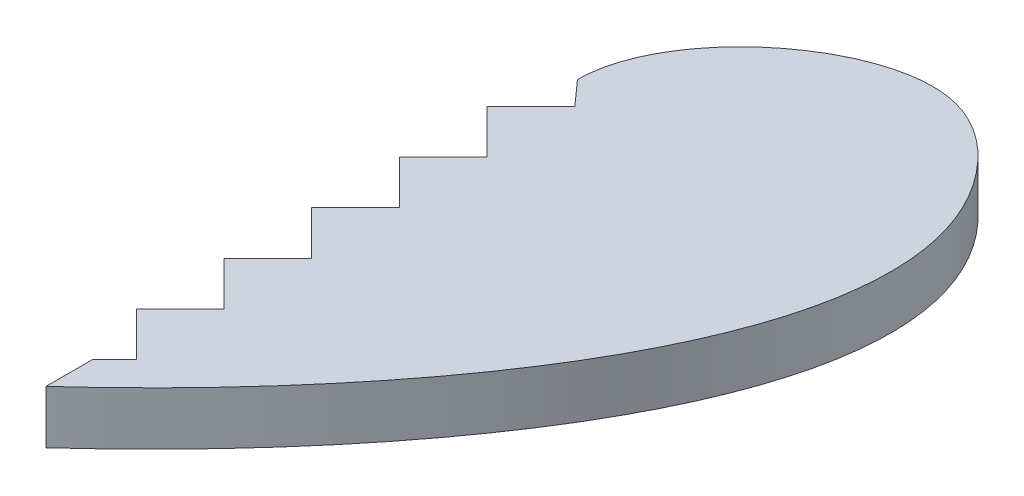
SolidWorks part; units mm, degrees
ref_plane "Front Plane" through (0, 0, 0) normal (0, 0, 1) x (1, 0, 0)
ref_plane "Top Plane" through (0, 0, 0) normal (0, 1, 0) x (1, 0, 0)
ref_plane "Right Plane" through (0, 0, 0) normal (1, 0, 0) x (0, 0, -1)
sketch "Sketch1" plane through (0, 0, 0) normal (0, 1, 0) x (1, 0, 0)
  line L0 (0, 14.0721) -> (0, -15.9279) construction
  line L1 (0, 10.7544) -> (0, 1.5585) construction
  line L2 (0, -55) -> (0, 55) construction
  spline S0 degree 3 poles (0, 14.0721) (0, 19.2449) (9.4205, 26.7564) (24.9138, 13.2722) (11.533, -5.4546) (0, -15.9279) knots 0 0 0 0 0.261667 0.361667 1 1 1 1
  spline S1 degree 3 poles (0, 14.0721) (0, 19.2449) (-9.4205, 26.7564) (-24.9138, 13.2722) (-11.533, -5.4546) (0, -15.9279) knots 0 0 0 0 0.261667 0.361667 1 1 1 1
  point P6 (0, 0)
  point P7 (0, 0)
  point P8 (0, 0)
  dimension "D1" = 30
extrude "Boss-Extrude1" add sketch "Sketch1" along normal blind 3
sketch "Sketch2" plane through (0, 3, 0) normal (0, 1, 0) x (1, 0, 0)
  line L0 (0, 14.0721) -> (1.2374, 12.684)
  line L1 (1.2374, -12.0648) -> (-1.2374, -14.5397)
  line L2 (1.2374, 12.684) -> (-1.2374, 10.2091)
  line L3 (-1.2374, 10.2091) -> (1.2374, 7.7342)
  line L4 (1.2374, 7.7342) -> (-1.2374, 5.2593)
  line L5 (-1.2374, 5.2593) -> (1.2374, 2.7845)
  line L6 (1.2374, 2.7845) -> (-1.2374, 0.3096)
  line L7 (-1.2374, 0.3096) -> (1.2374, -2.1653)
  line L8 (1.2374, -2.1653) -> (-1.2374, -4.6402)
  line L9 (-1.2374, -4.6402) -> (1.2374, -7.115)
  line L10 (1.2374, -7.115) -> (-1.2374, -9.5899)
  line L11 (-1.2374, -9.5899) -> (1.2374, -12.0648)
  line L12 (-1.2374, -14.5397) -> (0, -15.9279)
  line L13 (0, 14.0721) -> (0, -15.9279) construction
  spline S1 degree 3 poles (1514.8716, 1288.2661) (-463.8444, -281.802) (69.1877, -25.2608) (-11.6473, 45.0923) (-124.7996, -212.365) (1789.1499, 901.4783) knots -2.857633 -2.857633 -2.857633 -2.857633 0.638333 0.738333 2.359809 2.359809 2.359809 2.359809 only from (0, -15.9279) to (0, 14.0721) construction
  spline S2 degree 3 poles (0, -15.9279) (11.533, -5.4546) (24.9138, 13.2722) (9.4205, 26.7564) (0, 19.2449) (0, 14.0721) knots 0 0 0 0 0.638333 0.738333 1 1 1 1 construction
  spline S3 degree 3 poles (-1789.1544, 901.4809) (124.7997, -212.3654) (11.6473, 45.0924) (-69.1878, -25.2608) (463.845, -281.8022) (-1514.8746, 1288.2685) knots -1.35981 -1.35981 -1.35981 -1.35981 0.261667 0.361667 3.857635 3.857635 3.857635 3.857635 only from (0, 14.0721) to (0, -15.9279) construction
  spline S4 degree 3 poles (0, 14.0721) (0, 14.0723) (0, 14.0724) (0, 14.0725) knots 0 0 0 0 0.000006 0.000006 0.000006 0.000006
  spline S7 degree 3 poles (-2648.8668, 1411.9302) (154.0023, -280.0848) (14.9342, 47.953) (-75.4194, -30.6844) (590.452, -341.7944) (-2301.6412, 1905.5069) knots -1.57196 -1.57196 -1.57196 -1.57196 0.261667 0.361667 4.259851 4.259851 4.259851 4.259851 only from (0, 14.0721) to (0, -15.9279)
  spline S8 degree 3 poles (2301.6005, 1905.4753) (-590.4459, -341.7915) (75.4191, -30.6841) (-14.9346, 47.9534) (-154.0061, -280.0936) (2648.9864, 1412.0024) knots -3.259833 -3.259833 -3.259833 -3.259833 0.638333 0.738333 2.571986 2.571986 2.571986 2.571986 only from (0, -15.9279) to (0, 14.0721)
  spline S9 degree 3 poles (0, 14.0721) (0, 14.0723) (0, 14.0724) (0, 14.0725) knots 0 0 0 0 0.000006 0.000006 0.000006 0.000006
  spline S10 degree 3 poles (0, -15.9279) (11.533, -5.4546) (24.9138, 13.2722) (9.4205, 26.7564) (0, 19.2449) (0, 14.0721) knots 0 0 0 0 0.638333 0.738333 1 1 1 1
  point P17 (0, 11.4465)
  point P18 (0, -10.8274)
  dimension "D1" = 3.5
  dimension "D2" = 0
sketch "Sketch3" plane through (0, 3, 0) normal (0, 1, 0) x (1, 0, 0)
  line L15 (0, 14.0721) -> (1.2374, 12.684) construction
  line L17 (1.2374, 12.684) -> (-1.2374, 10.2091) construction
  line L18 (-1.2374, 10.2091) -> (1.2374, 7.7342) construction
  line L19 (1.2374, 7.7342) -> (-1.2374, 5.2593) construction
  line L20 (-1.2374, 5.2593) -> (1.2374, 2.7845) construction
  line L21 (1.2374, 2.7845) -> (-1.2374, 0.3096) construction
  line L22 (-1.2374, 0.3096) -> (1.2374, -2.1653) construction
  line L23 (1.2374, -2.1653) -> (-1.2374, -4.6402) construction
  line L24 (-1.2374, -4.6402) -> (1.2374, -7.115) construction
  line L25 (1.2374, -7.115) -> (-1.2374, -9.5899) construction
  line L26 (-1.2374, -9.5899) -> (1.2374, -12.0648) construction
  line L27 (0, 14.0721) -> (1.2374, 12.684)
  line L28 (1.2374, 12.684) -> (-1.2374, 10.2091)
  line L29 (-1.2374, 10.2091) -> (1.2374, 7.7342)
  line L30 (1.2374, 7.7342) -> (-1.2374, 5.2593)
  line L31 (-1.2374, 5.2593) -> (1.2374, 2.7845)
  line L32 (1.2374, 2.7845) -> (-1.2374, 0.3096)
  line L33 (-1.2374, 0.3096) -> (1.2374, -2.1653)
  line L34 (1.2374, -2.1653) -> (-1.2374, -4.6402)
  line L35 (-1.2374, -4.6402) -> (1.2374, -7.115)
  line L36 (1.2374, -7.115) -> (-1.2374, -9.5899)
  line L37 (-1.2374, -9.5899) -> (1.2374, -12.0648)
  line L38 (1.2374, -12.0648) -> (0, -13.3022)
  line L39 (1.2374, -12.0648) -> (-1.2374, -14.5397) construction
  line L40 (0, -13.3022) -> (0, -15.9279)
  spline S2 degree 3 poles (-1789.1544, 901.4809) (124.7997, -212.3654) (11.6473, 45.0924) (-69.1878, -25.2608) (463.845, -281.8022) (-1514.8746, 1288.2685) knots -1.35981 -1.35981 -1.35981 -1.35981 0.261667 0.361667 3.857635 3.857635 3.857635 3.857635 only from (0, 14.0721) to (0, -15.9279) construction
  spline S3 degree 3 poles (0, 14.0721) (0, 19.2449) (-9.4205, 26.7564) (-24.9138, 13.2722) (-11.533, -5.4546) (0, -15.9279) knots 0 0 0 0 0.261667 0.361667 1 1 1 1
extrude "Cut-Extrude1" cut sketch "Sketch3" against normal blind 3
